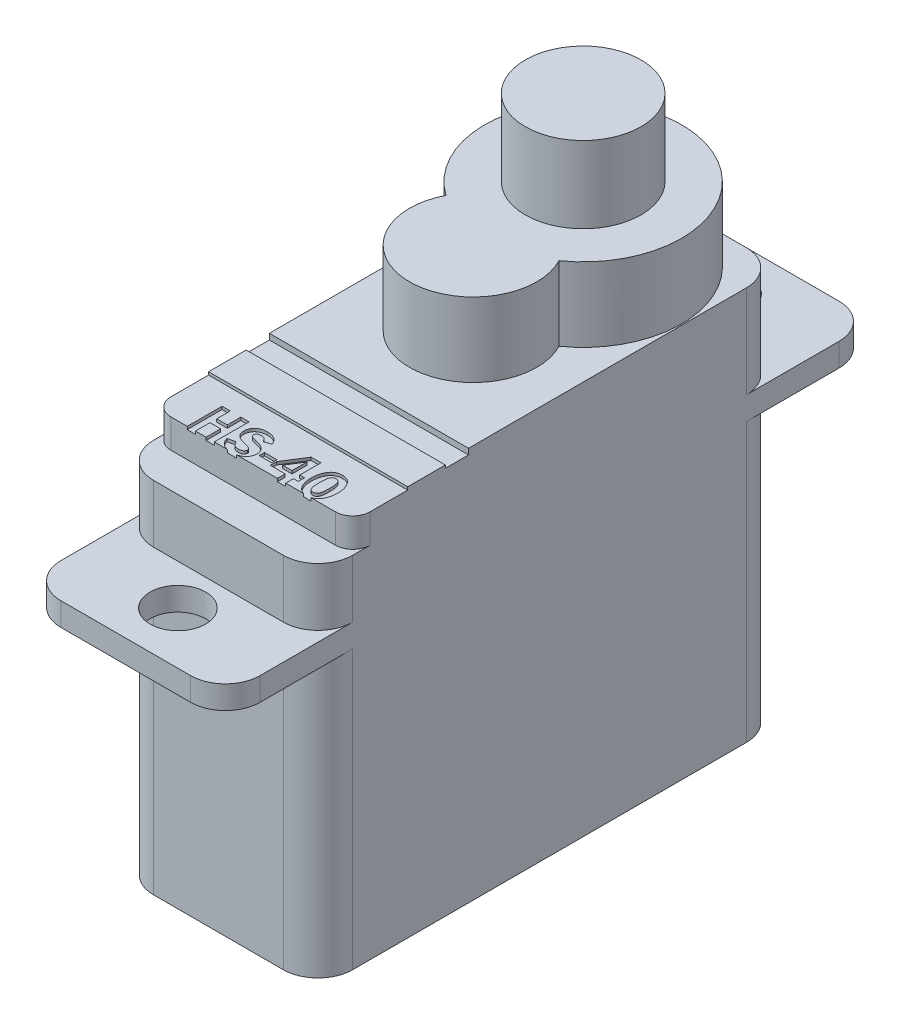
SolidWorks part; units mm, degrees
material "PLA (2)"
ref_plane "Front Plane" through (0, 0, 0) normal (0, 0, 1) x (1, 0, 0)
ref_plane "Top Plane" through (0, 0, 0) normal (0, 1, 0) x (1, 0, 0)
ref_plane "Right Plane" through (0, 0, 0) normal (1, 0, 0) x (0, 0, -1)
sketch "Sketch1" plane through (0, 0, 0) normal (0, 1, 0) x (1, 0, 0)
  line L1 (-4.3, -14) -> (4.3, -14)
  line L2 (-4.3, -14) -> (-4.3, 14)
  line L3 (-4.3, 14) -> (4.3, 14)
  line L4 (4.3, -14) -> (4.3, 14)
  line L5 (-4.3, -14) -> (4.3, 14) construction
  line L6 (-4.3, 14) -> (4.3, -14) construction
  point P0 (0, 0)
  dimension "D1" = 8.6
  dimension "D2" = 28
extrude "Boss-Extrude1" add sketch "Sketch1" along normal blind 1
sketch "Sketch2" plane through (0, 1, 0) normal (0, 1, 0) x (1, 0, 0)
  line L0 (4.3, -14) -> (4.3, 14) construction
  line L1 (-4.3, -10) -> (4.3, -10)
  line L2 (-4.3, -10) -> (-4.3, 10)
  line L3 (-4.3, 10) -> (4.3, 10)
  line L4 (4.3, -10) -> (4.3, 10)
  line L5 (-4.3, -10) -> (4.3, 10) construction
  line L6 (-4.3, 10) -> (4.3, -10) construction
  point P0 (0, 0)
  dimension "D1" = 20
extrude "Boss-Extrude2" add sketch "Sketch2" along normal blind 4
hole_wizard "M2 Clearance Hole1" positions "Sketch4" profile "Sketch5" hole size "M2" standard "AS" end condition through all
sketch "Sketch4" plane through (0, 1, 0) normal (0, 1, 0) x (1, 0, 0)
  line L0 (0, -11.75) -> (0, 11.75) construction
  point P0 (0, 11.75)
  point P2 (0, -11.75)
  dimension "D1" = 23.5
sketch "Sketch5" plane through (0, 1, -11.75) normal (1, 0, 0) x (0, 0, 1)
  line L0 (0, 0) -> (0, 1)
  line L1 (0, 1) -> (1.2, 1)
  line L2 (1.2, 1) -> (1.2, 0)
  line L5 (1.2, 0) -> (0, 0)
  line L11 (0, -6.35) -> (0, 107.95) construction
  dimension "Thru Hole Dia." = 2.4
  dimension "Thru Hole Depth" = 1
sketch "Sketch6" plane through (0, 5, 0) normal (0, 1, 0) x (1, 0, 0)
  line L0 (0, 11.75) -> (0, 5.75) construction
  line L2 (4.3, 10) -> (-4.3, 10) construction
  circle A0 centre (0, 5.75) radius 4.25
  dimension "D1" = 6
extrude "Boss-Extrude3" add sketch "Sketch6" along normal blind 3.2
sketch "Sketch7" plane through (0, 8.2, 0) normal (0, 1, 0) x (1, 0, 0)
  circle A0 centre (0, 5.75) radius 2.5
  dimension "D1" = 5
extrude "Boss-Extrude4" add sketch "Sketch7" along normal blind 3.3
sketch "Sketch8" plane through (0, 0, 0) normal (0, -1, 0) x (1, 0, 0)
  line L9 (4.3, 10) -> (-4.3, 10)
  line L10 (4.3, -10) -> (4.3, 10)
  line L11 (-4.3, -10) -> (4.3, -10)
  line L12 (-4.3, 10) -> (-4.3, -10)
  line L13 (4.3, 10) -> (-4.3, 10)
  line L14 (4.3, -10) -> (4.3, 10)
  line L15 (-4.3, -10) -> (4.3, -10)
  line L16 (-4.3, 10) -> (-4.3, -10)
  dimension "D1" = 0
extrude "Boss-Extrude5" add sketch "Sketch8" along normal blind 12
sketch "Sketch9" plane through (0, 5, 0) normal (0, 1, 0) x (1, 0, 0)
  line L0 (0, 1) -> (0, 0) construction
  circle A0 centre (0, 1) radius 2.75
  dimension "D1" = 5.5
  dimension "D2" = 1
extrude "Boss-Extrude6" add sketch "Sketch9" along normal up to surface (3.2 mm away) up to face at (0, 8.2, -3.25)
fillet "Fillet1" radius 1.5 12 edges at (-4.3, -6, -10) (-4.3, -6, 10) (-4.3, 3, -10) (4.3, 3, -10) (4.3, -6, -10) (4.3, -6, 10) (4.3, 3, 10) (-4.3, 3, 10) (-4.3, 0.5, 14) (4.3, 0.5, 14) (4.3, 0.5, -14) (-4.3, 0.5, -14)
sketch "Sketch10" plane through (0, 5, 0) normal (0, 1, 0) x (1, 0, 0)
  line L0 (4.3, -12.5) -> (4.3, -8.5) construction
  line L1 (-4.3, -8.5) -> (4.3, -8.5)
  line L2 (-4.3, -8.5) -> (-4.3, -10)
  line L3 (-4.3, -10) -> (4.3, -10)
  line L4 (4.3, -8.5) -> (4.3, -10)
  line L5 (-2.8, -10) -> (2.8, -10) construction
extrude "Cut-Extrude1" cut sketch "Sketch10" against normal blind 1.5
fillet "Fillet2" radius 0.75 2 edges at (-4.3, 4.25, 8.5) (4.3, 4.25, 8.5)
sketch "Sketch11" plane through (0, 5, 0) normal (0, 1, 0) x (1, 0, 0)
  line L0 (4.3, -7.75) -> (4.3, 8.5) construction
  line L1 (-4.3, -8.5) -> (4.3, -8.5)
  line L2 (-4.3, -8.5) -> (-4.3, -3.5)
  line L3 (-4.3, -3.5) -> (4.3, -3.5)
  line L4 (4.3, -8.5) -> (4.3, -3.5)
  dimension "D1" = 5
extrude "Cut-Extrude2" cut sketch "Sketch11" against normal blind 0.125
sketch "Sketch12" plane through (0, 4.875, 0) normal (0, 1, 0) x (1, 0, 0)
  line L0 (4.3, -7.75) -> (4.3, -3.5) construction
  line L1 (-4.3, -3.5) -> (4.3, -3.5)
  line L2 (-4.3, -3.5) -> (-4.3, -4.5)
  line L3 (-4.3, -4.5) -> (4.3, -4.5)
  line L4 (4.3, -3.5) -> (4.3, -4.5)
  dimension "D1" = 1
extrude "Cut-Extrude3" cut sketch "Sketch12" against normal blind 0.125
sketch "Sketch13" plane through (0, 4.875, 0) normal (0, 1, 0) x (1, 0, 0)
  line L0 (-4.3, -4.5) -> (-4.3, -7.75) construction
  line L1 (-4.3, -6.125) -> (4.3, -6.125)
  line L2 (-4.3, -6.125) -> (-4.3, -8.5)
  line L3 (-4.3, -8.5) -> (4.3, -8.5)
  line L4 (4.3, -6.125) -> (4.3, -8.5)
extrude "Cut-Extrude4" cut sketch "Sketch13" against normal blind 0.125
sketch "Sketch14" plane through (0, 4.75, 0) normal (0, 1, 0) x (1, 0, 0)
  text T0 "HS-40" font "Franklin Gothic Demi" height 1.5
extrude "Cut-Extrude5" cut sketch "Sketch14" against normal blind 0.125
sketch "Sketch15" plane through (0, 1, 0) normal (0, 1, 0) x (1, 0, 0)
  line L0 (0, 11.75) -> (0, -11.75) construction
  line L1 (-2.8, -10) -> (2.8, -10) construction
  line L2 (-2.8, -10) -> (2.8, -10) construction
  line L3 (2.8, 10) -> (-2.8, 10) construction
  line L4 (2.8, 10) -> (-2.8, 10) construction
  line L5 (4.3, -3.5) -> (4.3, 8.5) construction
  line L6 (-4.3, 8.5) -> (-4.3, -3.5) construction
  line L7 (4.3, -3.5) -> (4.3, 8.5) construction
  line L8 (-4.3, 8.5) -> (-4.3, -3.5) construction
  line L9 (-2.8, -14) -> (2.8, -14) construction
  line L10 (2.8, 14) -> (-2.8, 14) construction
  line L11 (-2.8, -14) -> (2.8, -14) construction
  line L12 (2.8, 14) -> (-2.8, 14) construction
  dimension "D1" = 8.6
  dimension "D2" = 20
  dimension "D3" = 23.5
  dimension "D4" = 28
move or copy body "Body-Move/Copy1" [suppressed] bodies to move or copy 115
